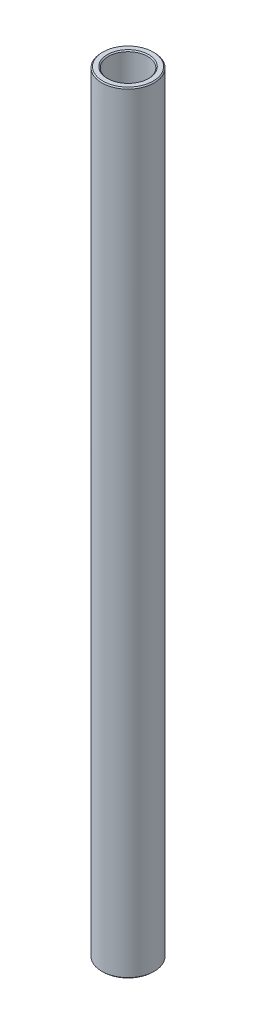
SolidWorks part; units mm, degrees
ref_plane "Front Plane" through (0, 0, 0) normal (0, 0, 1) x (1, 0, 0)
ref_plane "Top Plane" through (0, 0, 0) normal (0, 1, 0) x (1, 0, 0)
ref_plane "Right Plane" through (0, 0, 0) normal (1, 0, 0) x (0, 0, -1)
sketch "Sketch1" plane through (0, 0, 0) normal (0, 0, 1) x (1, 0, 0)
  line L0 (4.7625, 60.1594) -> (4.7625, 247.0619)
  line L1 (4.7625, 247.0619) -> (6.35, 247.0619)
  line L2 (6.35, 247.0619) -> (6.35, 60.1594)
  line L3 (6.35, 60.1594) -> (4.7625, 60.1594)
  line L4 (120.0875, 68.8906) -> (10.0875, 68.8906) construction
  line L6 (0, 50.6344) -> (0, 256.5869) construction
  dimension "D1" = 9.525
  dimension "D2" = 9.525
  dimension "D3" = 12.7
  dimension "D4" = 9.525
revolve "Revolve1" add sketch "Sketch1" angle 360 about L6
chamfer "Chamfer1" distance 0.254 angle 45 4 edges at (6.35, 247.0619, 0) (4.7625, 247.0619, 0) (4.7625, 60.1594, 0) (6.35, 60.1594, 0)
equation "\"D4@Sketch1\"=\"D1@Sketch1\""
